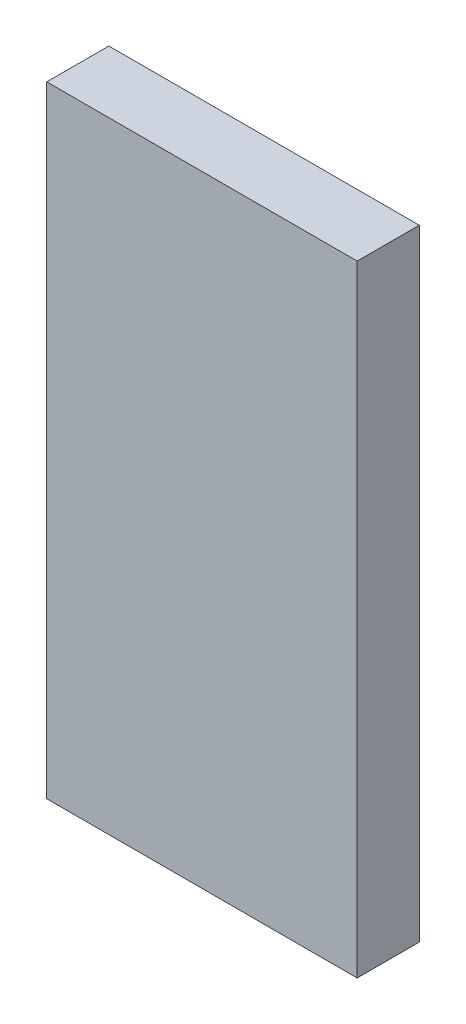
SolidWorks part; units mm, degrees
ref_plane "Front Plane" through (0, 0, 0) normal (0, 0, 1) x (1, 0, 0)
ref_plane "Top Plane" through (0, 0, 0) normal (0, 1, 0) x (1, 0, 0)
ref_plane "Right Plane" through (0, 0, 0) normal (1, 0, 0) x (0, 0, -1)
sketch "Sketch1" plane through (0, 0, 0) normal (0, 0, 1) x (1, 0, 0)
  line L1 (-30, 60) -> (30, 60)
  line L2 (-30, 60) -> (-30, -60)
  line L3 (-30, -60) -> (30, -60)
  line L4 (30, 60) -> (30, -60)
  line L5 (-30, 60) -> (30, -60) construction
  line L6 (-30, -60) -> (30, 60) construction
  point P0 (0, 0)
  dimension "D1" = 120
  dimension "D2" = 60
extrude "Boss-Extrude1" add sketch "Sketch1" along normal blind 12
